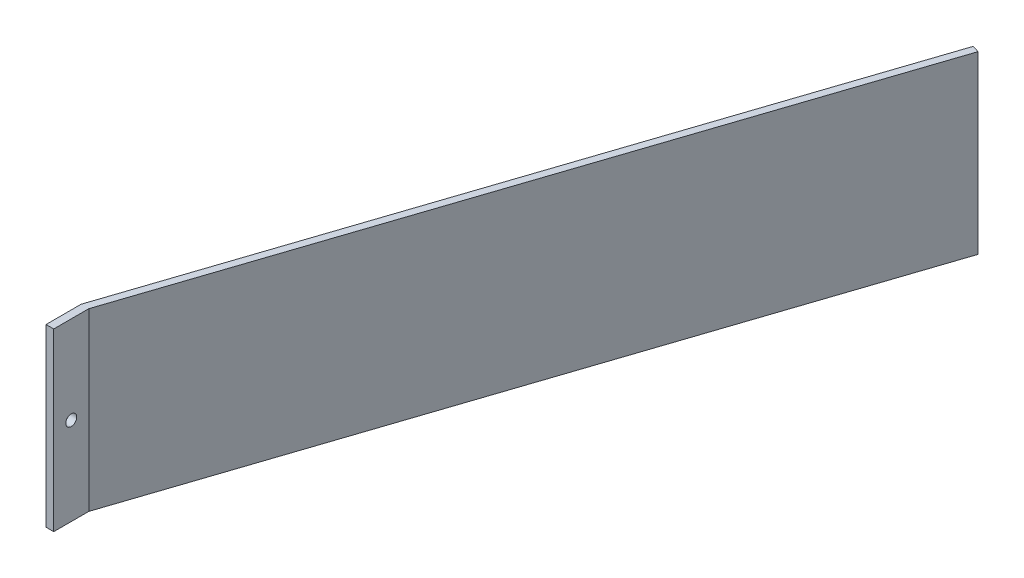
SolidWorks part; units mm, degrees
material "Acrylic (Medium-high impact)"
ref_plane "Front Plane" through (0, 0, 0) normal (0, 0, 1) x (1, 0, 0)
ref_plane "Top Plane" through (0, 0, 0) normal (0, 1, 0) x (1, 0, 0)
ref_plane "Right Plane" through (0, 0, 0) normal (1, 0, 0) x (0, 0, -1)
sketch "Sketch1" plane through (0, 0, 0) normal (0, 1, 0) x (1, 0, 0)
  line L0 (0, 152.4) -> (0, -152.4) construction
  line L1 (-279.4, -152.4) -> (279.4, -152.4) construction
  line L2 (-279.4, -152.4) -> (-279.4, 152.4) construction
  line L4 (279.4, -152.4) -> (279.4, 152.4) construction
  line L5 (-179.705, 152.4) -> (179.705, 152.4) construction
  line L6 (-279.4, 0) -> (279.4, 0) construction
  line L7 (-179.705, 152.4) -> (-279.4, 152.4) construction
  line L8 (179.705, 152.4) -> (279.4, 152.4) construction
  line L9 (-279.4, -137.16) -> (-182.7176, 153.4024)
  line L10 (-276.0538, -137.16) -> (-179.705, 152.4)
  line L11 (-274.5797, -122.6735) -> (-182.7176, 153.4024) construction
  line L12 (-271.5671, -123.676) -> (-179.705, 152.4) construction
  line L13 (-182.7176, 153.4024) -> (-179.705, 152.4)
  line L14 (-279.4, -137.16) -> (-279.4, -152.4)
  line L15 (-276.0538, -137.16) -> (-276.0538, -152.4)
  line L16 (-279.4, -152.4) -> (-276.0538, -152.4)
  line L17 (-279.4, -137.16) -> (-276.0538, -137.16) construction
  line L18 (-279.4, -144.78) -> (-276.0538, -144.78) construction
  point P0 (0, 0)
  point P12 (0, 152.4)
  dimension "D1" = 558.8
  dimension "D2" = 304.8
  dimension "D3" = 359.41
  dimension "D5" = 7.62
  dimension "D4" = 3.175
extrude "Boss-Extrude1" add sketch "Sketch1" along normal blind 76.2
sketch "Sketch2" plane through (-279.4, 0, 0) normal (-1, 0, 0) x (0, 0, 1)
  line L0 (144.78, 76.2) -> (144.78, 0) construction
  line L1 (137.16, 76.2) -> (152.4, 76.2) construction
  line L2 (137.16, 0) -> (152.4, 0) construction
  line L4 (137.16, 76.2) -> (137.16, 0) construction
  line L5 (137.16, 38.1) -> (152.4, 38.1) construction
  line L6 (152.4, 76.2) -> (152.4, 0) construction
  circle A0 centre (144.78, 38.1) radius 2.3813
  dimension "D1" = 4.7625
extrude "Cut-Extrude1" cut sketch "Sketch2" against normal through all both
sketch "Sketch3" plane through (-207.4469, 0, -69.0264) normal (0.9489, 0, 0.3157) x (0.3157, 0, -0.9489)
  line L0 (-13.732, 76.2) -> (49.768, 76.2)
  line L1 (-217.301, 76.2) -> (87.868, 76.2) construction
  line L2 (87.868, 76.2) -> (87.868, 0) construction
  line L3 (-217.301, 38.1) -> (87.868, 38.1) construction
  line L4 (-217.301, 76.2) -> (-217.301, 0) construction
  line L5 (-13.732, 0) -> (49.768, 0)
  arc A0 (-13.732, 76.2) -> (49.768, 76.2) centre (18.018, 138.5358) ccw
  arc A1 (-13.732, 0) -> (49.768, 0) centre (18.018, -62.3358) cw
  point P5 (18.018, 68.58)
  dimension "D1" = 63.5
  dimension "D2" = 38.1
  dimension "D3" = 7.62
extrude "Cut-Extrude2" [suppressed] cut sketch "Sketch3" against normal through all both
